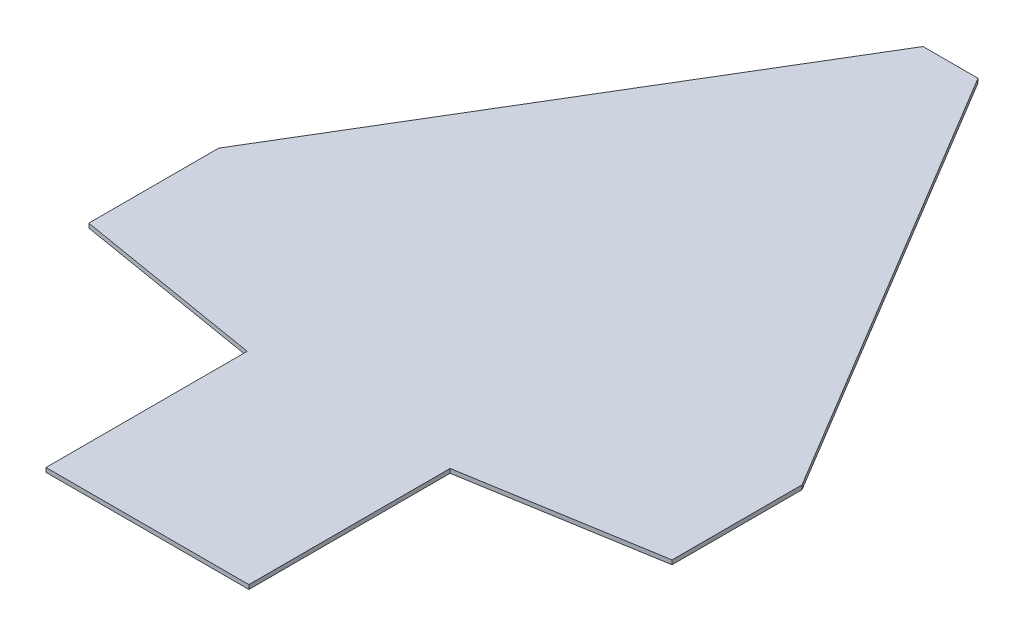
SolidWorks part; units mm, degrees
ref_plane "Front Plane" through (0, 0, 0) normal (0, 0, 1) x (1, 0, 0)
ref_plane "Top Plane" through (0, 0, 0) normal (0, 1, 0) x (1, 0, 0)
ref_plane "Right Plane" through (0, 0, 0) normal (1, 0, 0) x (0, 0, -1)
sketch "Sketch1" plane through (0, 0, 0) normal (0, 1, 0) x (1, 0, 0)
  line L6 (23.417, 69.5136) -> (23.417, -298.7864) construction
  line L7 (-215.343, -164.6932) -> (-215.343, -171.73)
  line L18 (39.9425, 82.2136) -> (6.8914, 82.2136)
  line L23 (-215.343, -164.6932) -> (-215.343, -294.8391) construction
  line L24 (-37.543, -279.4724) -> (-37.543, -400.3864)
  line L26 (-189.943, -171.73) -> (-215.343, -171.73)
  line L27 (-37.543, -400.3864) -> (84.377, -400.3864)
  line L28 (84.377, -400.3864) -> (84.377, -279.4724)
  line L30 (262.177, -294.8391) -> (88.5617, -323.8393) construction
  line L31 (-215.343, -294.8391) -> (-41.7278, -323.8393) construction
  line L32 (-62.943, 89.2504) -> (-62.943, 209.2136) construction
  line L33 (-62.943, 209.2136) -> (251.5885, 209.2136) construction
  line L34 (-62.943, 89.2504) -> (-215.343, -164.6932) construction
  line L35 (251.5885, 209.2136) -> (251.5885, 56.8136) construction
  line L36 (251.5885, 56.8136) -> (129.2433, 56.8136) construction
  line L37 (129.2433, 56.8136) -> (262.177, -164.6932) construction
  line L38 (262.177, -164.6932) -> (262.177, -294.8391) construction
  line L42 (6.8914, 82.2136) -> (-151.843, -182.2851)
  line L43 (226.1885, 82.2136) -> (84.377, 82.2136) construction
  line L44 (-151.843, -182.2851) -> (-151.843, -260.3801)
  line L51 (-37.543, 183.8136) -> (226.1885, 183.8136) construction
  line L52 (-37.543, 82.2136) -> (-37.543, 183.8136) construction
  line L66 (198.677, -182.2851) -> (198.677, -260.3801)
  line L67 (39.9425, 82.2136) -> (198.677, -182.2851)
  line L72 (-151.843, -260.3801) -> (-37.543, -279.4724)
  line L75 (-189.943, -273.33) -> (-37.543, -298.7864) construction
  line L77 (236.777, -273.33) -> (84.377, -298.7864) construction
  line L78 (198.677, -260.3801) -> (84.377, -279.4724)
  line L81 (51.1591, 75.8636) -> (-4.3252, 75.8636) construction
  line L82 (-0.7303, 69.5136) -> (-151.843, -182.2851) construction
  line L83 (47.5642, 69.5136) -> (198.677, -182.2851) construction
  line L84 (-151.843, -182.2851) -> (-151.843, -253.9422) construction
  line L85 (-37.543, 82.2136) -> (-189.943, -171.73) construction
  line L86 (-37.543, -285.9104) -> (-37.543, -400.3864) construction
  line L87 (84.377, 82.2136) -> (236.777, -171.73) construction
  line L88 (84.377, -400.3864) -> (84.377, -285.9104) construction
  line L89 (198.677, -182.2851) -> (198.677, -253.9422) construction
  line L90 (-158.193, -259.3195) -> (-31.193, -280.5331) construction
  line L91 (-189.943, -171.73) -> (-189.943, -273.33) construction
  line L92 (205.027, -259.3195) -> (78.027, -280.5331) construction
  line L93 (236.777, -171.73) -> (236.777, -273.33) construction
  line L121 (47.5642, 69.5136) -> (-0.7303, 69.5136) construction
  line L124 (54.754, 82.2136) -> (-7.9201, 82.2136) construction
  line L126 (226.1885, 183.8136) -> (226.1885, 82.2136) construction
  line L158 (51.1591, 75.8636) -> (205.027, -180.5259) construction
  line L159 (-4.3252, 75.8636) -> (-158.193, -180.5259) construction
  line L160 (-151.843, -253.9422) -> (-24.843, -275.1558) construction
  line L161 (-164.543, -264.6967) -> (-37.543, -285.9104) construction
  line L162 (-164.543, -178.7667) -> (-164.543, -264.6967) construction
  line L163 (-158.193, -180.5259) -> (-158.193, -259.3195) construction
  line L164 (211.377, -264.6967) -> (84.377, -285.9104) construction
  line L165 (211.377, -178.7667) -> (211.377, -264.6967) construction
  line L166 (205.027, -180.5259) -> (205.027, -259.3195) construction
  line L167 (198.677, -253.9422) -> (71.677, -275.1558) construction
  line L168 (-7.9201, 82.2136) -> (-164.543, -178.7667) construction
  line L169 (54.754, 82.2136) -> (211.377, -178.7667) construction
  line L170 (-31.193, -394.0364) -> (78.027, -394.0364) construction
  line L171 (-24.843, -387.6864) -> (71.677, -387.6864) construction
  line L172 (-31.193, -280.5331) -> (-31.193, -394.0364) construction
  line L173 (-24.843, -275.1558) -> (-24.843, -387.6864) construction
  line L174 (71.677, -387.6864) -> (71.677, -275.1558) construction
  line L175 (78.027, -394.0364) -> (78.027, -280.5331) construction
  dimension "D1" = 12.7
  dimension "D4" = 6.35
  dimension "D6" = 25.4
extrude "Boss-Extrude1" add sketch "Sketch1" along normal blind 2.54
